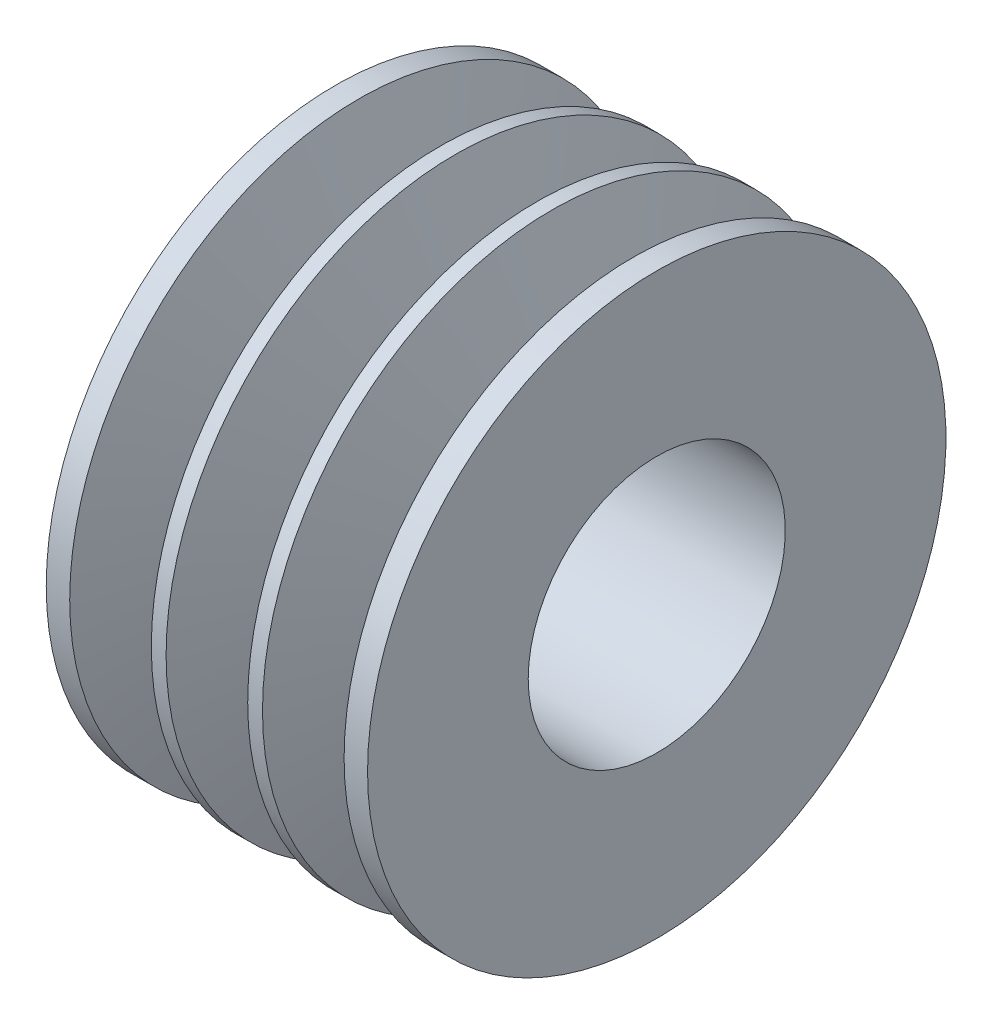
SolidWorks part; units mm, degrees
ref_plane "Ebene vorne" through (0, 0, 0) normal (0, 0, 1) x (1, 0, 0)
ref_plane "Ebene oben" through (0, 0, 0) normal (0, 1, 0) x (1, 0, 0)
ref_plane "Ebene rechts" through (0, 0, 0) normal (1, 0, 0) x (0, 0, -1)
sketch "Skizze1" plane through (0, 0, 0) normal (0, 0, 1) x (1, 0, 0)
  line L0 (24.8218, 25.9746) -> (123.6689, 25.9746) construction
  line L1 (45.0996, 45.9746) -> (95.0996, 45.9746)
  line L2 (95.0996, 45.9746) -> (95.0996, 70.9746)
  line L3 (45.0996, 45.9746) -> (45.0996, 70.9746)
  line L4 (95.0996, 70.9746) -> (91.4496, 70.9746)
  line L5 (91.4496, 70.9746) -> (87.2306, 57.1746)
  line L6 (85.0996, 98.4087) -> (85.0996, 70.0723) construction
  line L7 (78.7496, 70.9746) -> (82.9687, 57.1746)
  line L8 (82.9687, 57.1746) -> (87.2306, 57.1746)
  line L9 (70.0996, 99.9404) -> (70.0996, 74.103) construction
  line L10 (78.7496, 70.9746) -> (76.4496, 70.9746)
  line L11 (76.4496, 70.9746) -> (72.2306, 57.1746)
  line L12 (72.2306, 57.1746) -> (70.0996, 57.1746)
  line L13 (63.7496, 70.9746) -> (67.9687, 57.1746)
  line L14 (61.4496, 70.9746) -> (63.7496, 70.9746)
  line L15 (61.4496, 70.9746) -> (57.2306, 57.1746)
  line L16 (57.2306, 57.1746) -> (52.9687, 57.1746)
  line L17 (48.7496, 70.9746) -> (52.9687, 57.1746)
  line L18 (45.0996, 70.9746) -> (48.7496, 70.9746)
  line L19 (67.9687, 57.1746) -> (70.0996, 57.1746)
  dimension "D1" = 25
  dimension "D2" = 20
  dimension "D3" = 13.8
  dimension "D4" = 10
  dimension "D5" = 17
  dimension "D6" = 12.7
  dimension "D7" = 17
  dimension "D8" = 25
  dimension "D9" = 15
revolve "Rotation2" add sketch "Skizze1" angle 360 about L0
